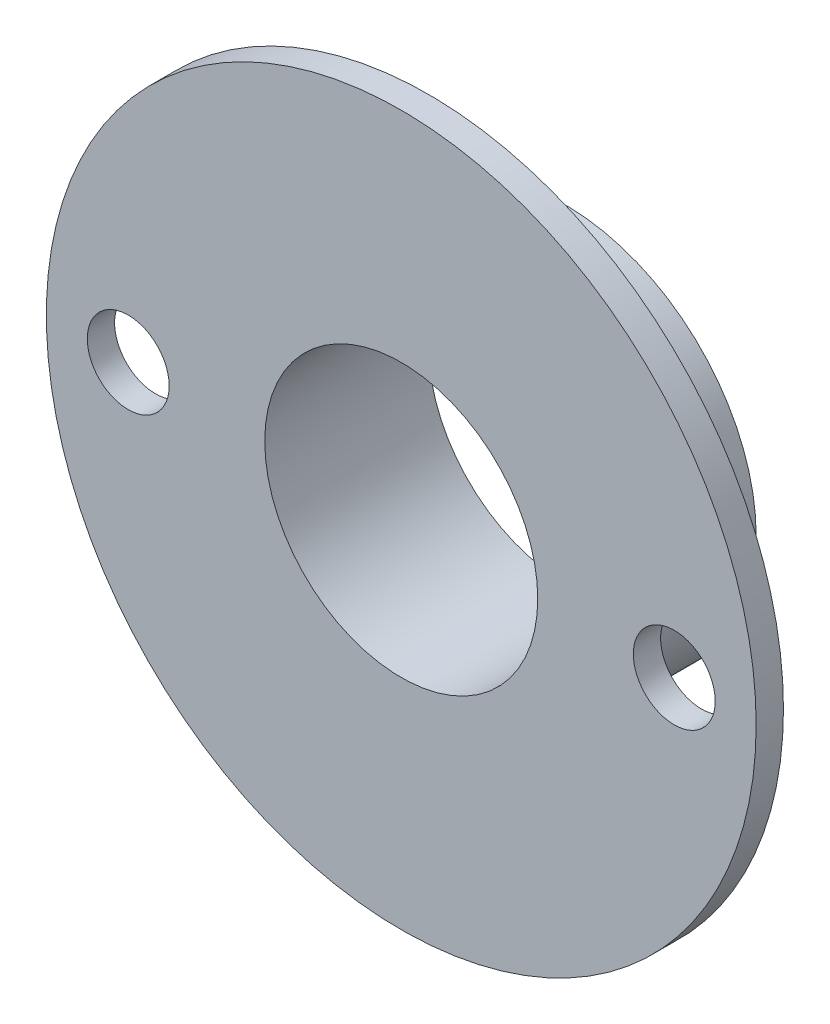
SolidWorks part; units mm, degrees
material "Copper"
ref_plane "Front Plane" through (0, 0, 0) normal (0, 0, 1) x (1, 0, 0)
ref_plane "Top Plane" through (0, 0, 0) normal (0, 1, 0) x (1, 0, 0)
ref_plane "Right Plane" through (0, 0, 0) normal (1, 0, 0) x (0, 0, -1)
sketch "Sketch1" plane through (0, 0, 0) normal (0, 0, 1) x (1, 0, 0)
  circle A0 centre (0, 0) radius 5
  circle A1 centre (0, 0) radius 7
  dimension "D1" = 10
  dimension "D2" = 14
extrude "Boss-Extrude1" add sketch "Sketch1" along normal blind 6
sketch "Sketch2" plane through (0, 0, 6) normal (0, 0, 1) x (1, 0, 0)
  circle A0 centre (0, 0) radius 7
  circle A1 centre (0, 0) radius 13
  dimension "D1" = 14
  dimension "D2" = 26
extrude "Boss-Extrude2" add sketch "Sketch2" against normal blind 1 contours A1 | A0
sketch "Sketch3" plane through (0, 0, 6) normal (0, 0, 1) x (1, 0, 0)
  circle A0 centre (-10, 0) radius 1.5
  circle A1 centre (10, 0) radius 1.5
  dimension "D1" = 10
  dimension "D3" = 3
  dimension "D4" = 3
  dimension "D2" = 10
extrude "Cut-Extrude1" cut sketch "Sketch3" against normal blind 1
